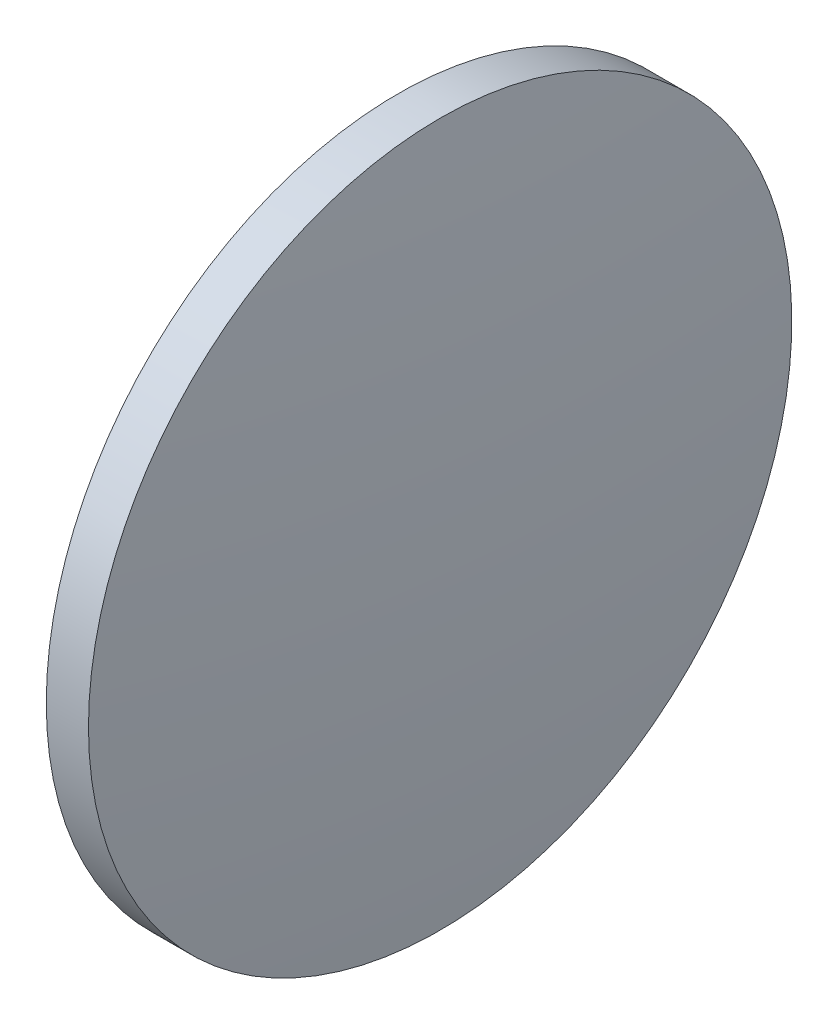
SolidWorks part; units mm, degrees
ref_plane "前视基准面" through (0, 0, 0) normal (0, 0, 1) x (1, 0, 0)
ref_plane "上视基准面" through (0, 0, 0) normal (0, 1, 0) x (1, 0, 0)
ref_plane "右视基准面" through (0, 0, 0) normal (1, 0, 0) x (0, 0, -1)
sketch "草图1" plane through (0, 0, 0) normal (0, 0, 1) x (1, 0, 0)
  line L0 (457.8596, 88.8713) -> (478.1482, 88.8713) construction
  line L1 (462.0046, 88.8713) -> (462.0046, 113.8713)
  line L2 (462.0046, 113.8713) -> (465.0046, 113.8713)
  line L3 (466.2146, 88.8713) -> (462.0046, 88.8713)
  arc A0 (466.2146, 88.8713) -> (465.0046, 113.8713) centre (207.3452, 88.8713) ccw
revolve "旋转1" add sketch "草图1" angle 360 about L0
